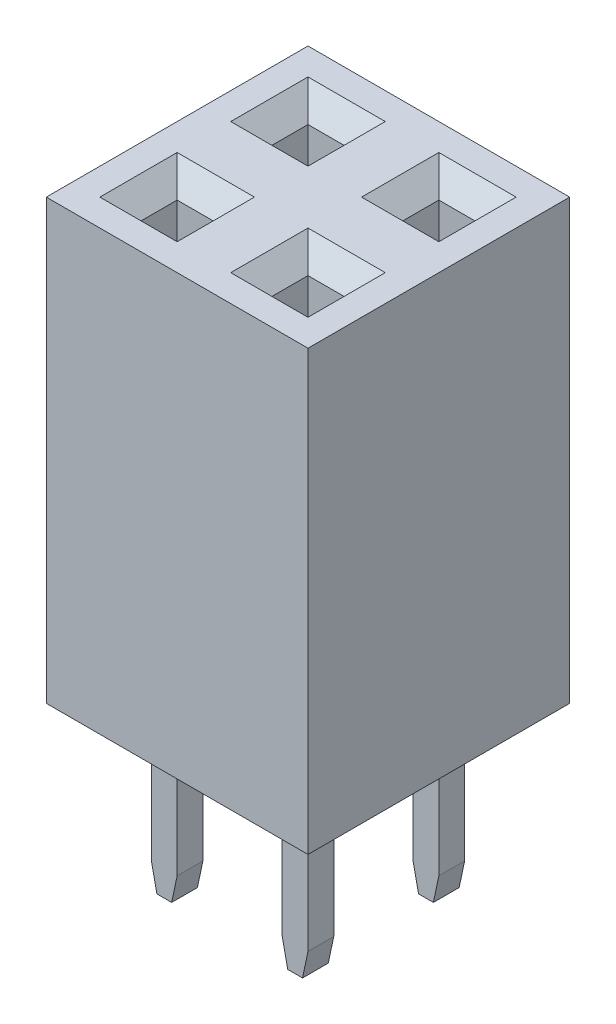
SolidWorks part; units mm, degrees
ref_plane "Спереди" through (0, 0, 0) normal (0, 0, 1) x (1, 0, 0)
ref_plane "Сверху" through (0, 0, 0) normal (0, 1, 0) x (1, 0, 0)
ref_plane "Справа" through (0, 0, 0) normal (1, 0, 0) x (0, 0, -1)
ref_plane "Плоскость1" through (0, 0, 0) normal (0, 1, 0) x (-1, 0, 0)
sketch "Эскиз1" plane through (0, 0, 0) normal (0, 1, 0) x (-1, 0, 0)
  line L0 (0, 0) -> (-5.5295, 0) construction
  line L1 (0, 0) -> (0, -2.1715) construction
  line L2 (-1.27, 1.27) -> (1.27, 1.27)
  line L3 (-1.27, 1.27) -> (-1.27, -1.27)
  line L4 (-1.27, -1.27) -> (1.27, -1.27)
  line L5 (1.27, 1.27) -> (1.27, -1.27)
  point P0 (-1.27, 1.27)
  point P1 (1.27, -1.27)
  point P2 (-1.27, -1.27)
  point P3 (1.27, 1.27)
  dimension "D1" = 2.54
  dimension "D6" = 1.27
extrude "Бобышка-Вытянуть1" add sketch "Эскиз1" along normal blind 8.51
sketch "Эскиз4" plane through (0, 8.51, 0) normal (0, 1, 0) x (1, 0, 0)
  line L0 (0, 0) -> (0.806, 0) construction
  line L1 (0, 0) -> (0, 1.2961) construction
  line L3 (-0.35, 0.35) -> (0.35, 0.35)
  line L4 (-0.35, 0.35) -> (-0.35, -0.35)
  line L5 (-0.35, -0.35) -> (0.35, -0.35)
  line L6 (0.35, 0.35) -> (0.35, -0.35)
  dimension "D1" = 0.7
extrude "Вырез-Вытянуть1" cut sketch "Эскиз4" against normal blind 8.21
chamfer "Фаска3" distance 0.4 angle 45 4 edges at (0.35, 8.51, 0) (0, 8.51, -0.35) (0, 8.51, 0.35) (-0.35, 8.51, 0)
sketch "Эскиз2" plane through (0, 0, 0) normal (0, 1, 0) x (-1, 0, 0)
  line L0 (0, 0) -> (0, -0.4454) construction
  line L1 (0.25, 0.25) -> (-0.25, 0.25)
  line L2 (0.25, 0.25) -> (0.25, -0.25)
  line L3 (0.25, -0.25) -> (-0.25, -0.25)
  line L4 (-0.25, 0.25) -> (-0.25, -0.25)
  line L5 (0, 0) -> (-0.4704, 0) construction
  dimension "D1" = 0.5
  dimension "D2" = 0.5
extrude "Бобышка-Вытянуть2" add sketch "Эскиз2" against normal blind 3.15
chamfer "Фаска2" distance 0.5 angle 12 2 edges at (0.25, -3.15, 0) (-0.25, -3.15, 0)
pattern_linear "Линейный массив1" count 2 spacing 2.54 along (0, 0, -1) count 2 spacing 2.54 along (-1, 0, 0) of "Бобышка-Вытянуть1", "Вырез-Вытянуть1", "Фаска3", "Бобышка-Вытянуть2", "Фаска2"
equation "\"D6@Эскиз1\"=2.54/2"
